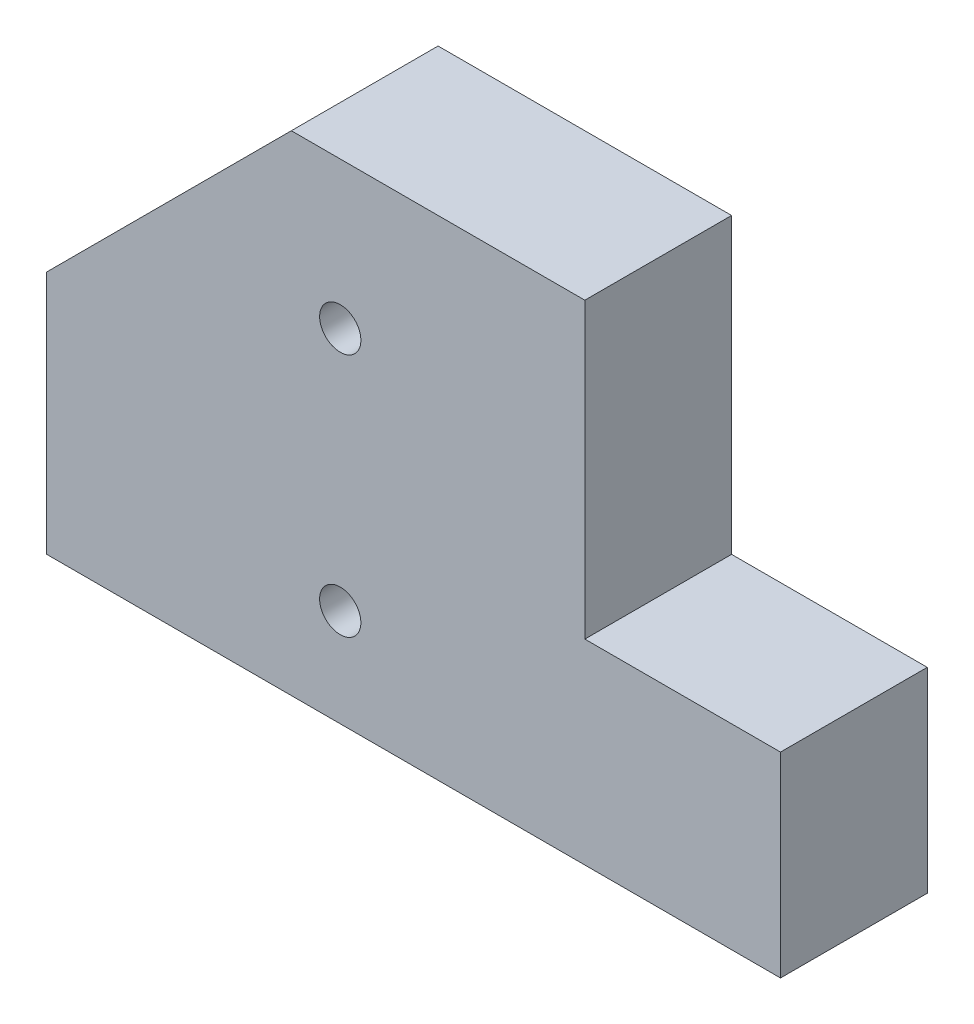
SolidWorks part; units mm, degrees
ref_plane "Alzado" through (0, 0, 0) normal (0, 0, 1) x (1, 0, 0)
ref_plane "Planta" through (0, 0, 0) normal (0, 1, 0) x (1, 0, 0)
ref_plane "Vista lateral" through (0, 0, 0) normal (1, 0, 0) x (0, 0, -1)
sketch "Croquis1" plane through (0, 0, 0) normal (0, 0, 1) x (1, 0, 0)
  line L0 (0, 0) -> (0, 50)
  line L1 (0, 50) -> (50, 100)
  line L2 (50, 100) -> (110, 100)
  line L3 (110, 100) -> (110, 40)
  line L4 (110, 40) -> (150, 40)
  line L5 (150, 40) -> (150, 0)
  line L6 (150, 0) -> (0, 0)
  dimension "D1" = 50
  dimension "D2" = 40
  dimension "D3" = 150
  dimension "D4" = 100
  dimension "D5" = 135
  dimension "D6" = 60
extrude "Saliente-Extruir1" add sketch "Croquis1" along normal blind 30
sketch "Croquis3" plane through (0, 0, 30) normal (0, 0, 1) x (1, 0, 0)
  line L0 (110, 100) -> (50, 100) construction
  line L1 (110, 40) -> (110, 100) construction
  point P0 (60, 70)
  point P1 (60, 20)
  point P4 (110, 70)
  dimension "D1" = 50
  dimension "D2" = 30
  dimension "D3" = 50
hole_wizard "Taladro de margen para 5/161" positions "Croquis3D2" profile "Croquis4" hole size "5/16" standard "Ansi Inch"
sketch3d "Croquis3D2"
  point P0 (60, 70, 30)
  point P3 (60, 20, 30)
sketch "Croquis4" plane through (60, 70, 30) normal (1, 0, 0) x (0, -1, 0)
  line L0 (0, 0) -> (0, 27.9335)
  line L1 (0, 27.9335) -> (4.2164, 25.4)
  line L2 (4.2164, 25.4) -> (4.2164, 0)
  line L5 (4.2164, 0) -> (0, 0)
  line L10 (0, 27.9335) -> (-4.2164, 25.4) construction
  line L11 (0, -6.35) -> (0, 107.95) construction
  dimension "Diámetro de taladro" = 8.4328
  dimension "Profundidad de taladro" = 25.4
  dimension "Ángulo de perforador" = 118
